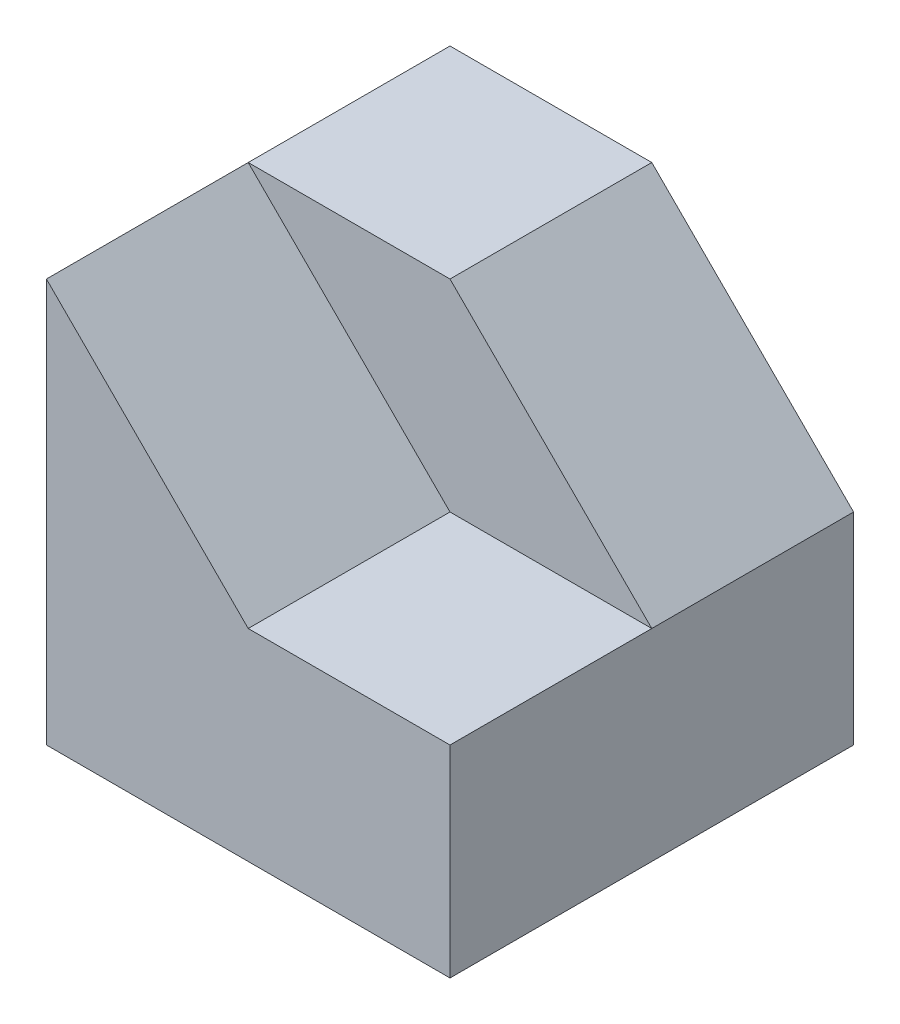
SolidWorks part; units mm, degrees
ref_plane "Alzado" through (0, 0, 0) normal (0, 0, 1) x (1, 0, 0)
ref_plane "Planta" through (0, 0, 0) normal (0, 1, 0) x (1, 0, 0)
ref_plane "Vista lateral" through (0, 0, 0) normal (1, 0, 0) x (0, 0, -1)
sketch "Croquis1" plane through (0, 0, 0) normal (0, 0, 1) x (1, 0, 0)
  line L0 (0, 60) -> (0, 0)
  line L1 (0, 0) -> (60, 0)
  line L2 (60, 0) -> (60, 30)
  line L3 (60, 30) -> (30, 60)
  line L4 (30, 60) -> (0, 60)
  dimension "D1" = 60
  dimension "D2" = 30
extrude "Saliente-Extruir1" add sketch "Croquis1" against normal blind 60
sketch "Croquis2" plane through (0, 0, 0) normal (0, 0, 1) x (1, 0, 0)
  line L0 (60, 30) -> (30, 60) construction
  line L1 (30, 60) -> (0, 60) construction
  line L2 (60, 30) -> (30, 60)
  line L3 (30, 60) -> (0, 60)
  line L4 (0, 60) -> (30, 30)
  line L5 (30, 30) -> (60, 30)
extrude "Cortar-Extruir1" cut sketch "Croquis2" against normal blind 30
